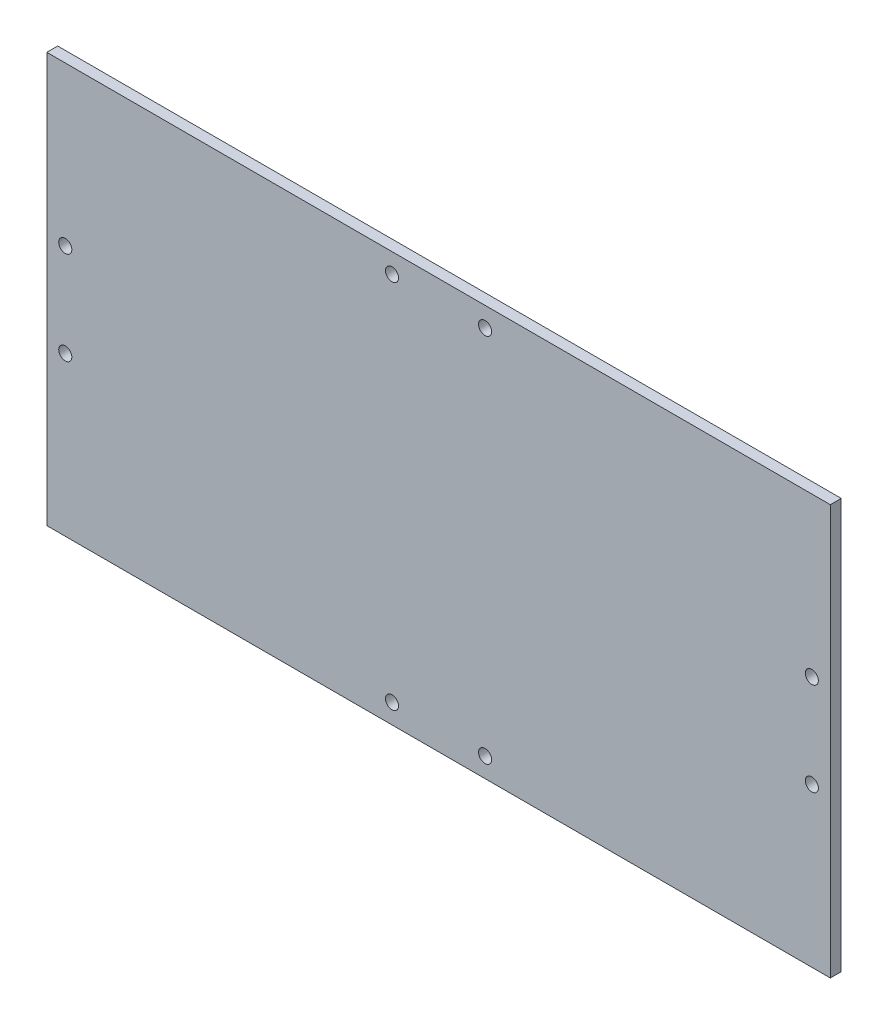
SolidWorks part; units mm, degrees
material "6061-T6 (SS)"
ref_plane "Front Plane" through (0, 0, 0) normal (0, 0, 1) x (1, 0, 0)
ref_plane "Top Plane" through (0, 0, 0) normal (0, 1, 0) x (1, 0, 0)
ref_plane "Right Plane" through (0, 0, 0) normal (1, 0, 0) x (0, 0, -1)
sketch "Sketch1" plane through (0, 0, 0) normal (0, 0, 1) x (1, 0, 0)
  line L0 (-108.712, 13.5509) -> (-108.712, -13.5509) construction
  line L1 (-114.0968, -59.69) -> (114.0968, -59.69)
  line L2 (-114.0968, -59.69) -> (-114.0968, 59.69)
  line L3 (-114.0968, 59.69) -> (114.0968, 59.69)
  line L4 (114.0968, -59.69) -> (114.0968, 59.69)
  line L5 (-114.0968, -59.69) -> (114.0968, 59.69) construction
  line L6 (-114.0968, 59.69) -> (114.0968, -59.69) construction
  line L7 (-108.712, 0) -> (-114.0968, 0) construction
  line L8 (0, 0) -> (0, 59.69) construction
  line L9 (0, -24.588) -> (0, 0) construction
  line L10 (-32.75, -24.588) -> (32.75, -24.588) construction
  line L11 (-32.75, -24.588) -> (-32.75, 6.762) construction
  line L12 (-32.75, 6.762) -> (32.75, 6.762) construction
  line L13 (32.75, -24.588) -> (32.75, 6.762) construction
  line L14 (0, -18.288) -> (0, -24.588) construction
  line L15 (-58, -2.938) -> (58, -2.938) construction
  line L16 (-58, -2.938) -> (-58, -18.288) construction
  line L17 (-58, -18.288) -> (58, -18.288) construction
  line L18 (58, -2.938) -> (58, -18.288) construction
  line L19 (-13.5509, 53.975) -> (13.5509, 53.975) construction
  line L20 (-54.2, -17.018) -> (54.2, -17.018) construction
  line L21 (-54.2, -17.018) -> (-54.2, -4.208) construction
  line L22 (-54.2, -4.208) -> (54.2, -4.208) construction
  line L23 (54.2, -17.018) -> (54.2, -4.208) construction
  line L24 (-54.2, -17.018) -> (54.2, -4.208) construction
  line L25 (-54.2, -4.208) -> (54.2, -17.018) construction
  line L26 (0, 0) -> (-108.712, 0) construction
  circle A0 centre (-108.712, 13.5509) radius 1.905
  circle A1 centre (-108.712, -13.5509) radius 1.905
  circle A2 centre (108.712, -13.5509) radius 1.905
  circle A3 centre (108.712, 13.5509) radius 1.905
  circle A4 centre (-32.75, 6.762) radius 1.2 construction
  circle A5 centre (32.75, 6.762) radius 1.2 construction
  circle A6 centre (32.75, -24.588) radius 1.2 construction
  circle A7 centre (-32.75, -24.588) radius 1.2 construction
  circle A8 centre (-13.5509, 53.975) radius 1.905
  circle A9 centre (13.5509, 53.975) radius 1.905
  circle A10 centre (13.5509, -53.975) radius 1.905
  circle A11 centre (-13.5509, -53.975) radius 1.905
  point P31 (0, -10.613)
  dimension "D3" = 108.712
  dimension "D6" = 31.35
  dimension "D9" = 41.402
  dimension "D4" = 3.81
  dimension "D8" = 2.4
  dimension "D1" = 228.1936
  dimension "D2" = 119.38
  dimension "D5" = 27.1018
  dimension "D7" = 65.5
  dimension "D10" = 6.3
  dimension "D11" = 15.35
  dimension "D12" = 116
  dimension "D13" = 108.4
  dimension "D14" = 1.27
  dimension "D15" = 1.27
  dimension "D16" = 13.5509
  dimension "D17" = 5.715
extrude "Boss-Extrude1" add sketch "Sketch1" along normal blind 3.175
